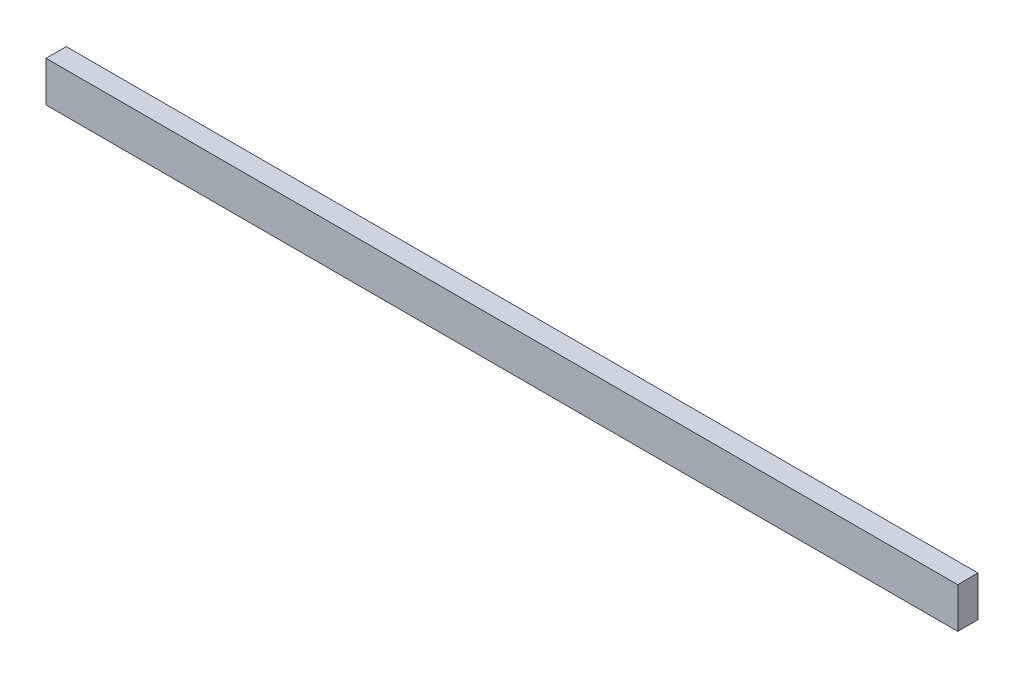
SolidWorks part; units mm, degrees
material "Erable"
ref_plane "Plan de face" through (0, 0, 0) normal (0, 0, 1) x (1, 0, 0)
ref_plane "Plan de dessus" through (0, 0, 0) normal (0, 1, 0) x (1, 0, 0)
ref_plane "Plan de droite" through (0, 0, 0) normal (1, 0, 0) x (0, 0, -1)
sketch "Esquisse1" plane through (0, 0, 0) normal (0, 0, 1) x (1, 0, 0)
  line L1 (-338, 15) -> (338, 15)
  line L2 (-338, 15) -> (-338, -15)
  line L3 (-338, -15) -> (338, -15)
  line L4 (338, 15) -> (338, -15)
  line L5 (-338, 15) -> (338, -15) construction
  line L6 (-338, -15) -> (338, 15) construction
  point P0 (0, 0)
  dimension "D1" = 676
  dimension "D2" = 30
extrude "Boss.-Extru.1" add sketch "Esquisse1" along normal blind 15
